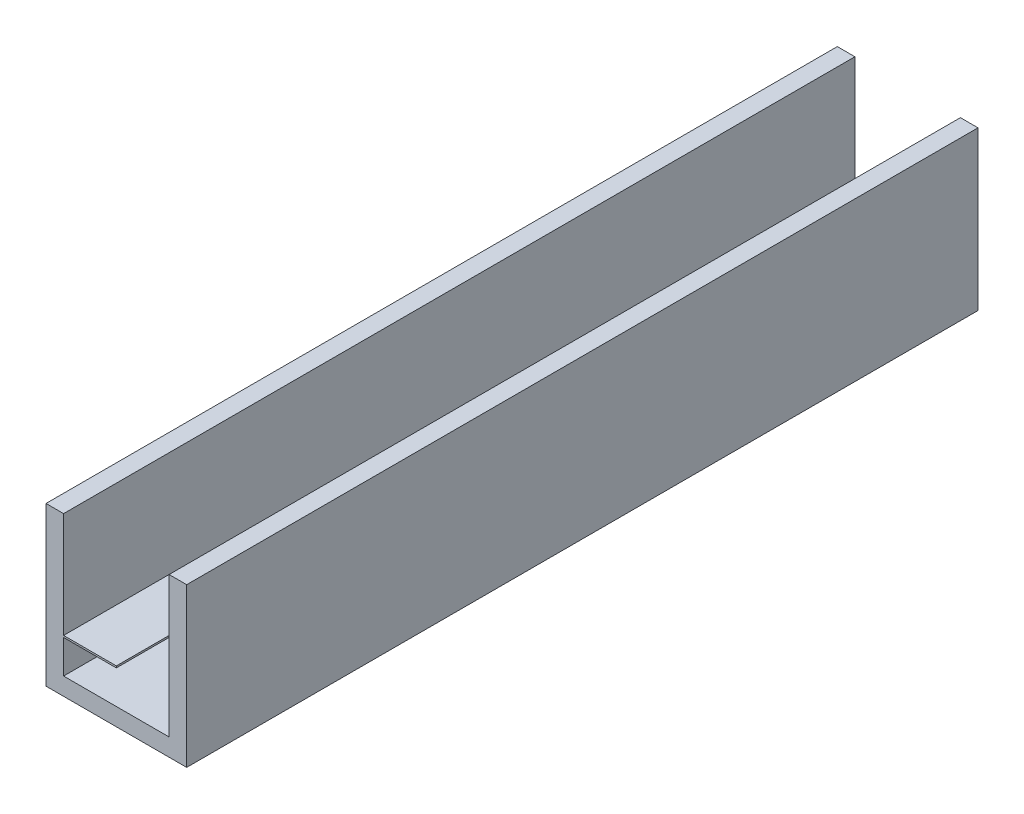
SolidWorks part; units mm, degrees
ref_plane "Alzado" through (0, 0, 0) normal (0, 0, 1) x (1, 0, 0)
ref_plane "Planta" through (0, 0, 0) normal (0, 1, 0) x (1, 0, 0)
ref_plane "Vista lateral" through (0, 0, 0) normal (1, 0, 0) x (0, 0, -1)
sketch "Croquis1" plane through (0, 0, 0) normal (0, 0, 1) x (1, 0, 0)
  line L0 (0, 0) -> (-800, 0)
  line L1 (0, 0) -> (0, 900)
  line L2 (-800, 0) -> (-800, 900)
  line L3 (-700, 100) -> (-100, 100)
  line L4 (-100, 100) -> (-100, 900)
  line L5 (-100, 900) -> (0, 900)
  line L6 (-700, 100) -> (-700, 900)
  line L7 (-700, 900) -> (-800, 900)
  point P11 (-100, 500)
  dimension "D1" = 800
  dimension "D2" = 900
  dimension "D3" = 900
  dimension "D4" = 100
  dimension "D5" = 100
  dimension "D6" = 100
extrude "Saliente-Extruir1" add sketch "Croquis1" along normal blind 4500
sketch "Croquis2" plane through (0, 0, 0) normal (0, 0, -1) x (-1, 0, 0)
  line L1 (700, 100) -> (700, 900) construction
  line L2 (700, 290) -> (400, 290)
  line L3 (400, 290) -> (400, 300)
  line L4 (400, 300) -> (700, 300)
  line L5 (700, 300) -> (700, 290)
  dimension "D2" = 300
  dimension "D3" = 10
extrude "Saliente-Extruir2" add sketch "Croquis2" against normal up to surface (4500 mm away) up to face at (-400, 475, 4500)
